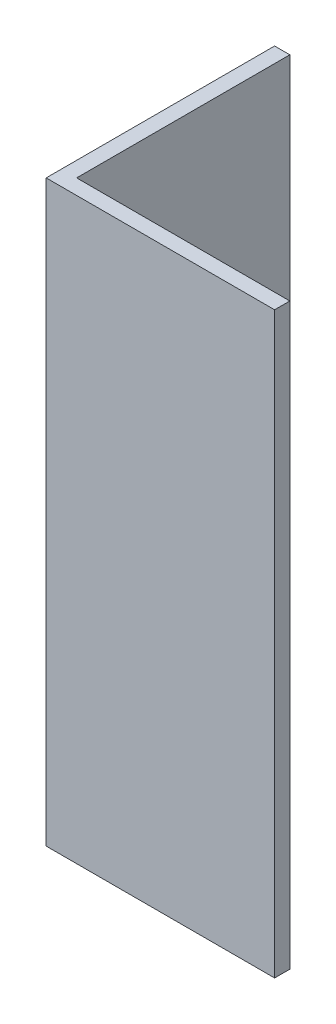
SolidWorks part; units mm, degrees
material "1060 Сплав"
ref_plane "Спереди" through (0, 0, 0) normal (0, 0, 1) x (1, 0, 0)
ref_plane "Сверху" through (0, 0, 0) normal (0, 1, 0) x (1, 0, 0)
ref_plane "Справа" through (0, 0, 0) normal (1, 0, 0) x (0, 0, -1)
sketch "Эскиз1" plane through (0, 0, 0) normal (0, 1, 0) x (1, 0, 0)
  line L0 (0, 0) -> (0, 15)
  line L1 (0, 15) -> (1, 15)
  line L2 (1, 15) -> (1, 1)
  line L3 (1, 1) -> (15, 1)
  line L4 (15, 1) -> (15, 0)
  line L5 (15, 0) -> (0, 0)
  dimension "D1" = 1
  dimension "D2" = 15
extrude "Бобышка-Вытянуть1" add sketch "Эскиз1" along normal blind 38
